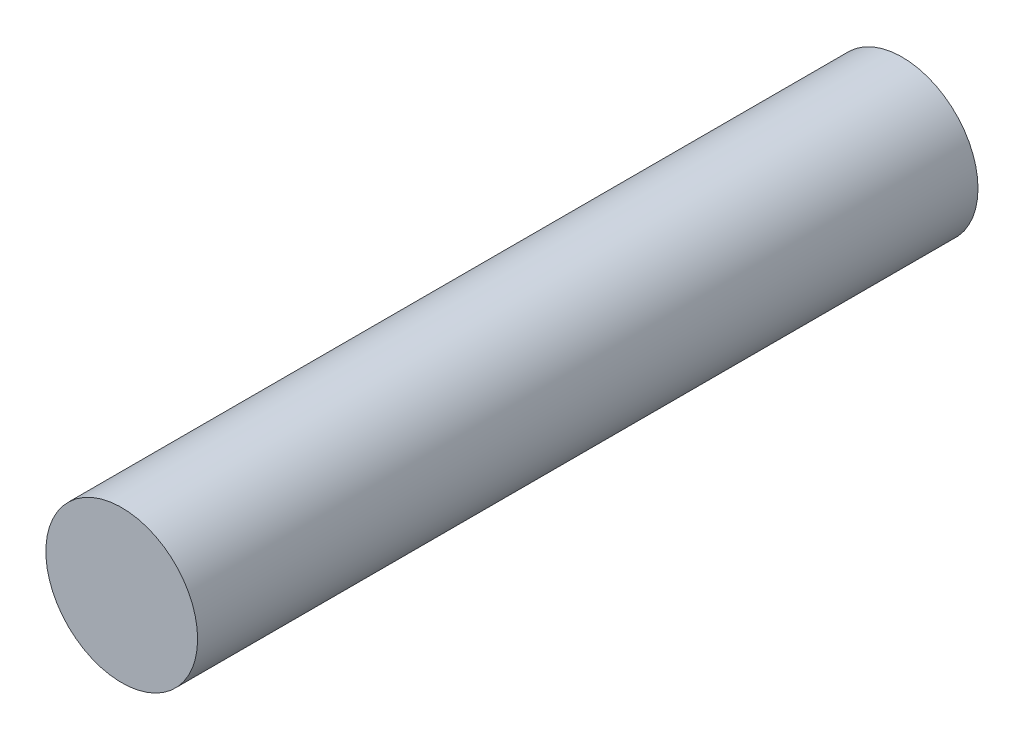
SolidWorks part; units mm, degrees
ref_plane "Alzado" through (0, 0, 0) normal (0, 0, 1) x (1, 0, 0)
ref_plane "Planta" through (0, 0, 0) normal (0, 1, 0) x (1, 0, 0)
ref_plane "Vista lateral" through (0, 0, 0) normal (1, 0, 0) x (0, 0, -1)
sketch "Croquis1" plane through (0, 0, 0) normal (0, 0, 1) x (1, 0, 0)
  circle A0 centre (0, 0) radius 3.5
extrude "Saliente-Extruir1" add sketch "Croquis1" along normal blind 36
